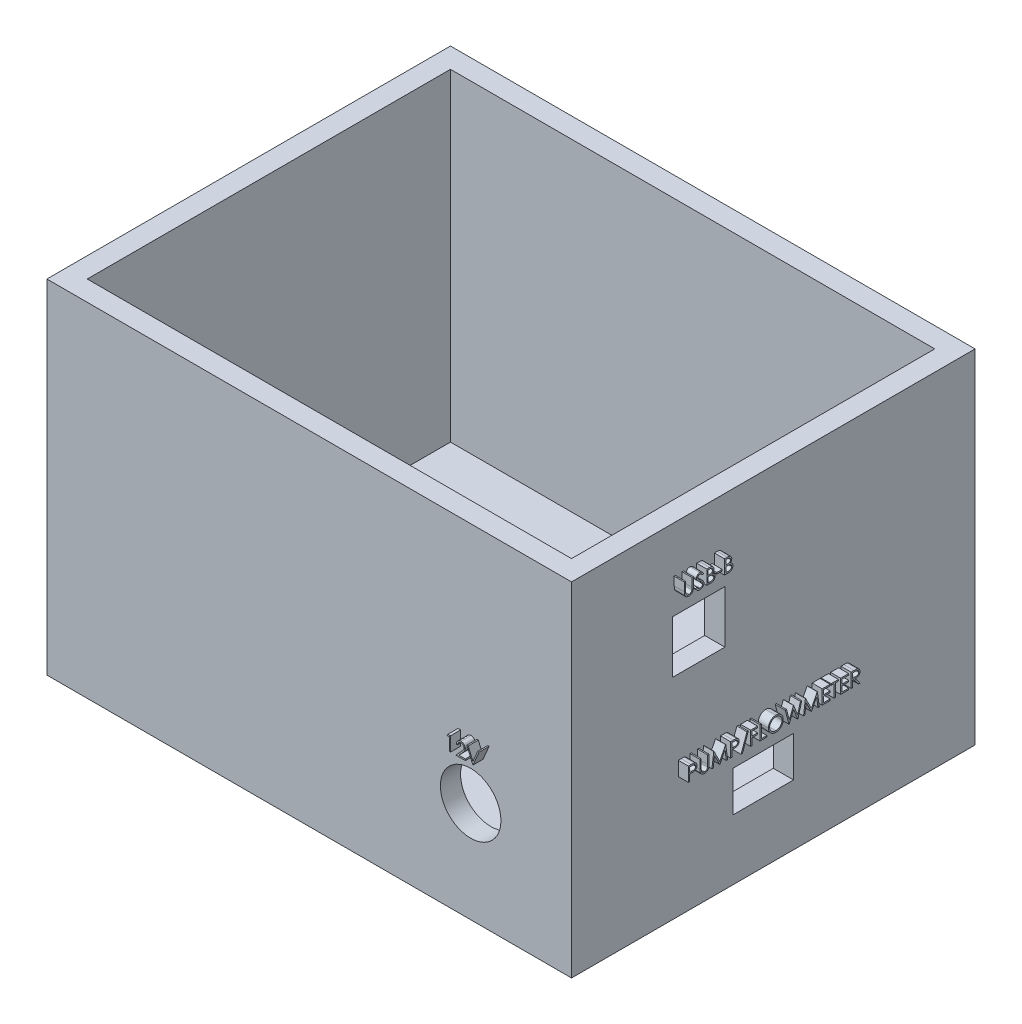
SolidWorks part; units mm, degrees
ref_plane "Front Plane" through (0, 0, 0) normal (0, 0, 1) x (1, 0, 0)
ref_plane "Top Plane" through (0, 0, 0) normal (0, 1, 0) x (1, 0, 0)
ref_plane "Right Plane" through (0, 0, 0) normal (1, 0, 0) x (0, 0, -1)
sketch "Sketch1" plane through (0, 0, 0) normal (0, 1, 0) x (1, 0, 0)
  line L1 (-60, -45) -> (60, -45)
  line L2 (-60, -45) -> (-60, 45)
  line L3 (-60, 45) -> (60, 45)
  line L4 (60, -45) -> (60, 45)
  line L5 (-60, -45) -> (60, 45) construction
  line L6 (-60, 45) -> (60, -45) construction
  line L7 (-65, -50) -> (65, -50)
  line L8 (-65, -50) -> (-65, 50)
  line L9 (-65, 50) -> (65, 50)
  line L10 (65, -50) -> (65, 50)
  line L11 (-65, -50) -> (65, 50) construction
  line L12 (-65, 50) -> (65, -50) construction
  point P0 (0, 0)
  point P6 (0, 0)
  dimension "D1" = 120
  dimension "D2" = 90
  dimension "D3" = 5
  dimension "D4" = 5
extrude "Boss-Extrude1" add sketch "Sketch1" along normal blind 80
sketch "Sketch3" plane through (0, 0, 0) normal (0, -1, 0) x (1, 0, 0)
  line L1 (-65, -50) -> (65, -50)
  line L2 (-65, -50) -> (-65, 50)
  line L3 (-65, 50) -> (65, 50)
  line L4 (65, -50) -> (65, 50)
  line L5 (-65, -50) -> (65, 50) construction
  line L6 (-65, 50) -> (65, -50) construction
  point P0 (0, 0)
extrude "Boss-Extrude3" add sketch "Sketch3" along normal blind 5
sketch "Sketch4" plane through (0, 0, 50) normal (0, 0, 1) x (1, 0, 0)
  line L0 (65, -5) -> (-65, -5) construction
  line L2 (65, 80) -> (65, -5) construction
  circle A0 centre (40, 20) radius 7.5
  dimension "D1" = 15
  dimension "D2" = 25
  dimension "D3" = 25
extrude "Cut-Extrude1" cut sketch "Sketch4" against normal up to surface (5 mm away) up to face at (0, 40, 45)
sketch "Sketch5" plane through (0, 0, 50) normal (0, 0, 1) x (1, 0, 0)
  line L1 (65, 80) -> (65, -5) construction
  circle A0 centre (40, 20) radius 7.5 construction
  text T0 "12V"
  dimension "D1" = 11
  dimension "D2" = 29
extrude "Boss-Extrude4" add sketch "Sketch5" along normal blind 2.5
sketch "Sketch8" plane through (65, 0, 0) normal (1, 0, 0) x (0, 0, -1)
  line L0 (-50, 80) -> (-50, -5) construction
  line L1 (-25, 47) -> (-12, 47)
  line L2 (-25, 47) -> (-25, 60)
  line L3 (-25, 60) -> (-12, 60)
  line L4 (-12, 47) -> (-12, 60)
  line L6 (-50, 80) -> (50, 80) construction
  dimension "D1" = 13
  dimension "D2" = 13
  dimension "D3" = 25
  dimension "D4" = 20
extrude "Cut-Extrude3" cut sketch "Sketch8" against normal up to next
sketch "Sketch9" plane through (65, 0, 0) normal (1, 0, 0) x (0, 0, -1)
  line L0 (-12, 60) -> (-25, 60) construction
  line L1 (-25, 60) -> (-25, 47) construction
  text T0 "USB-B"
  dimension "D1" = 5
  dimension "D2" = 0
extrude "Boss-Extrude6" add sketch "Sketch9" along normal blind 2.5
sketch "Sketch10" plane through (0, -5, 0) normal (0, -1, 0) x (1, 0, 0)
  line L1 (65, -50) -> (65, 50) construction
  line L2 (-65, 50) -> (-65, -50) construction
  circle A0 centre (30, 0) radius 2.5
  circle A1 centre (-30, 0) radius 2.5
  dimension "D1" = 5
  dimension "D4" = 5
  dimension "D2" = 0
  dimension "D3" = 35
  dimension "D5" = 35
extrude "Cut-Extrude4" cut sketch "Sketch10" against normal up to next
sketch "Sketch11" plane through (0, -5, 0) normal (0, -1, 0) x (1, 0, 0)
  circle A0 centre (-30, 0) radius 2.5 construction
  text T0 "LED"
  dimension "D1" = 5
  dimension "D2" = 3.5
extrude "Cut-Extrude5" cut sketch "Sketch11" against normal blind 2.5
sketch "Sketch12" plane through (0, -5, 0) normal (0, -1, 0) x (1, 0, 0)
  circle A0 centre (30, 0) radius 2.5 construction
  text T0 "PHOTO"
  text T1 "SENSOR"
  dimension "D1" = 5
  dimension "D2" = 8
  dimension "D3" = 10
  dimension "D4" = 7
extrude "Cut-Extrude6" cut sketch "Sketch12" against normal blind 2.5
sketch "Sketch13" plane through (65, 0, 0) normal (1, 0, 0) x (0, 0, -1)
  line L0 (50, 80) -> (50, -5) construction
  line L1 (-10, 20) -> (5, 20)
  line L2 (-10, 20) -> (-10, 10)
  line L3 (-10, 10) -> (5, 10)
  line L4 (5, 20) -> (5, 10)
  line L5 (50, -5) -> (-50, -5) construction
  dimension "D1" = 10
  dimension "D2" = 15
  dimension "D3" = 45
  dimension "D4" = 15
extrude "Cut-Extrude7" cut sketch "Sketch13" against normal up to next
sketch "Sketch14" plane through (65, 0, 0) normal (1, 0, 0) x (0, 0, -1)
  line L0 (5, 20) -> (-10, 20) construction
  line L1 (-10, 20) -> (-10, 10) construction
  text T0 "PUMP/FLOWMETER"
  dimension "D1" = 5
  dimension "D2" = 14
extrude "Boss-Extrude7" add sketch "Sketch14" along normal blind 2.5
